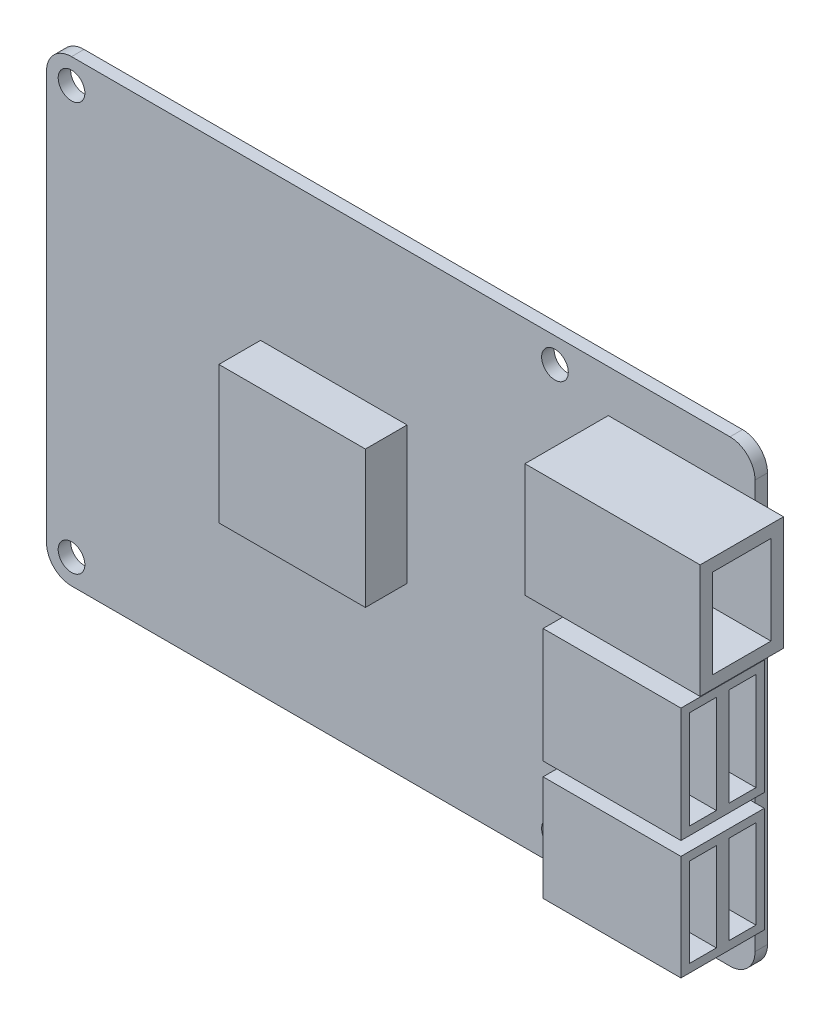
SolidWorks part; units mm, degrees
ref_plane "Front Plane" through (0, 0, 0) normal (0, 0, 1) x (1, 0, 0)
ref_plane "Top Plane" through (0, 0, 0) normal (0, 1, 0) x (1, 0, 0)
ref_plane "Right Plane" through (0, 0, 0) normal (1, 0, 0) x (0, 0, -1)
sketch "Sketch1" plane through (0, 0, 0) normal (0, 0, 1) x (1, 0, 0)
  line L0 (4.3421, -1.9236) -> (89.3421, -1.9236) construction
  line L1 (7.3421, 25.5764) -> (86.3421, 25.5764)
  line L2 (4.3421, 22.5764) -> (4.3421, -26.4236)
  line L3 (7.3421, -29.4236) -> (86.3421, -29.4236)
  line L4 (89.3421, 22.5764) -> (89.3421, -26.4236)
  circle A0 centre (7.3421, 22.5764) radius 1.6
  circle A1 centre (7.3421, -26.4236) radius 1.6
  circle A2 centre (7.3421, 22.5764) radius 1.6
  circle A3 centre (7.3421, -26.4236) radius 1.6
  circle A4 centre (7.3421, 22.5764) radius 1.6
  circle A5 centre (7.3421, -26.4236) radius 1.6
  circle A6 centre (7.3421, 22.5764) radius 1.6
  circle A7 centre (7.3421, -26.4236) radius 1.6
  circle A8 centre (65.3421, -26.4236) radius 1.6
  circle A9 centre (65.3421, 22.5764) radius 1.6
  circle A10 centre (65.3421, -26.4236) radius 1.6
  circle A11 centre (65.3421, 22.5764) radius 1.6
  circle A12 centre (65.3421, -26.4236) radius 1.6
  circle A13 centre (65.3421, 22.5764) radius 1.6
  circle A14 centre (65.3421, -26.4236) radius 1.6
  circle A15 centre (65.3421, 22.5764) radius 1.6
  arc A16 (86.3421, 25.5764) -> (89.3421, 22.5764) centre (86.3421, 22.5764) cw
  arc A17 (86.3421, -29.4236) -> (89.3421, -26.4236) centre (86.3421, -26.4236) ccw
  arc A18 (7.3421, 25.5764) -> (4.3421, 22.5764) centre (7.3421, 22.5764) ccw
  arc A19 (4.3421, -26.4236) -> (7.3421, -29.4236) centre (7.3421, -26.4236) ccw
  point P32 (89.3421, 25.5764)
  point P35 (89.3421, -29.4236)
  point P38 (4.3421, 25.5764)
  dimension "D6" = 3
  dimension "D2" = 55
extrude "Boss-Extrude1" add sketch "Sketch1" along normal blind 1.5 contours L4 L1 L2 L3 A1 A0 A8 A9 | L0 L2 A19 L3 A17 L4 A8 A1
sketch "Sketch2" plane through (0, 0, 1.5) normal (0, 0, 1) x (1, 0, 0)
  line L1 (71.7387, 20.4772) -> (92.7595, 20.4772)
  line L2 (71.7387, 20.4772) -> (71.7387, 6.8085)
  line L3 (71.7387, 6.8085) -> (92.7595, 6.8085)
  line L4 (92.7595, 20.4772) -> (92.7595, 6.8085)
  line L5 (73.917, 4.445) -> (90.4556, 4.445)
  line L6 (73.917, 4.445) -> (73.917, -9.32)
  line L7 (73.917, -9.32) -> (90.4556, -9.32)
  line L8 (90.4556, 4.445) -> (90.4556, -9.32)
  line L9 (73.917, -10.9636) -> (90.4556, -10.9636)
  line L10 (73.917, -10.9636) -> (73.917, -23.5987)
  line L11 (73.917, -23.5987) -> (90.4556, -23.5987)
  line L12 (90.4556, -10.9636) -> (90.4556, -23.5987)
extrude "Boss-Extrude2" add sketch "Sketch2" along normal blind 10
sketch "Sketch3" plane through (0, 0, 1.5) normal (0, 0, 1) x (1, 0, 0)
  line L1 (47.6007, 7.435) -> (30.0205, 7.435)
  line L2 (47.6007, 7.435) -> (47.6007, -9.0289)
  line L3 (47.6007, -9.0289) -> (30.0205, -9.0289)
  line L4 (30.0205, 7.435) -> (30.0205, -9.0289)
extrude "Boss-Extrude3" add sketch "Sketch3" along normal blind 5
sketch "Sketch4" plane through (92.7595, 0, 0) normal (1, 0, 0) x (0, 0, -1)
  line L8 (-3, 8.3085) -> (-3, 18.9772)
  line L9 (-3, 18.9772) -> (-10, 18.9772)
  line L10 (-10, 18.9772) -> (-10, 8.3085)
  line L11 (-10, 8.3085) -> (-3, 8.3085)
  line L12 (-3, 8.3085) -> (-3, 18.9772)
  line L13 (-3, 18.9772) -> (-10, 18.9772)
  line L14 (-10, 18.9772) -> (-10, 8.3085)
  line L15 (-10, 8.3085) -> (-3, 8.3085)
  dimension "D1" = 1.5
extrude "Cut-Extrude1" cut sketch "Sketch4" against normal blind 15
sketch "Sketch5" plane through (90.4556, 0, 0) normal (1, 0, 0) x (0, 0, -1)
  line L0 (-6.5, -23.5987) -> (-6.5, 4.445) construction
  line L1 (-11.5, -23.5987) -> (-1.5, -23.5987) construction
  line L2 (-11.5, 4.445) -> (-1.5, 4.445) construction
  line L19 (-2.5, -22.5987) -> (-2.5, -11.9636)
  line L20 (-2.5, -11.9636) -> (-10.5, -11.9636)
  line L21 (-10.5, -11.9636) -> (-10.5, -22.5987)
  line L22 (-10.5, -22.5987) -> (-2.5, -22.5987)
  line L23 (-2.5, -22.5987) -> (-2.5, -11.9636)
  line L24 (-2.5, -11.9636) -> (-5.75, -11.9636)
  line L25 (-10.5, -11.9636) -> (-10.5, -22.5987)
  line L26 (-10.5, -22.5987) -> (-7.25, -22.5987)
  line L27 (-5.75, -22.5987) -> (-5.75, -11.9636)
  line L28 (-7.25, -22.5987) -> (-7.25, -11.9636)
  line L29 (-5.75, -23.5987) -> (-5.75, 4.445) construction
  line L30 (-5.75, -22.5987) -> (-2.5, -22.5987)
  line L31 (-2.5, -8.32) -> (-2.5, 3.445)
  line L32 (-2.5, 3.445) -> (-10.5, 3.445)
  line L33 (-10.5, 3.445) -> (-10.5, -8.32)
  line L34 (-10.5, -8.32) -> (-2.5, -8.32)
  line L35 (-2.5, -8.32) -> (-2.5, 3.445)
  line L36 (-2.5, 3.445) -> (-5.75, 3.445)
  line L37 (-10.5, 3.445) -> (-10.5, -8.32)
  line L38 (-10.5, -8.32) -> (-7.25, -8.32)
  line L39 (-7.25, -23.5987) -> (-7.25, 4.445) construction
  line L40 (-7.25, -11.9636) -> (-10.5, -11.9636)
  line L41 (-7.25, -8.32) -> (-7.25, 3.445)
  line L42 (-5.75, -8.32) -> (-5.75, 3.445)
  line L43 (-5.75, -8.32) -> (-2.5, -8.32)
  line L44 (-7.25, 3.445) -> (-10.5, 3.445)
  dimension "D1" = 1
  dimension "D2" = 1
  dimension "D3" = 0.75
  dimension "D4" = 0.75
extrude "Cut-Extrude2" cut sketch "Sketch5" against normal blind 15
